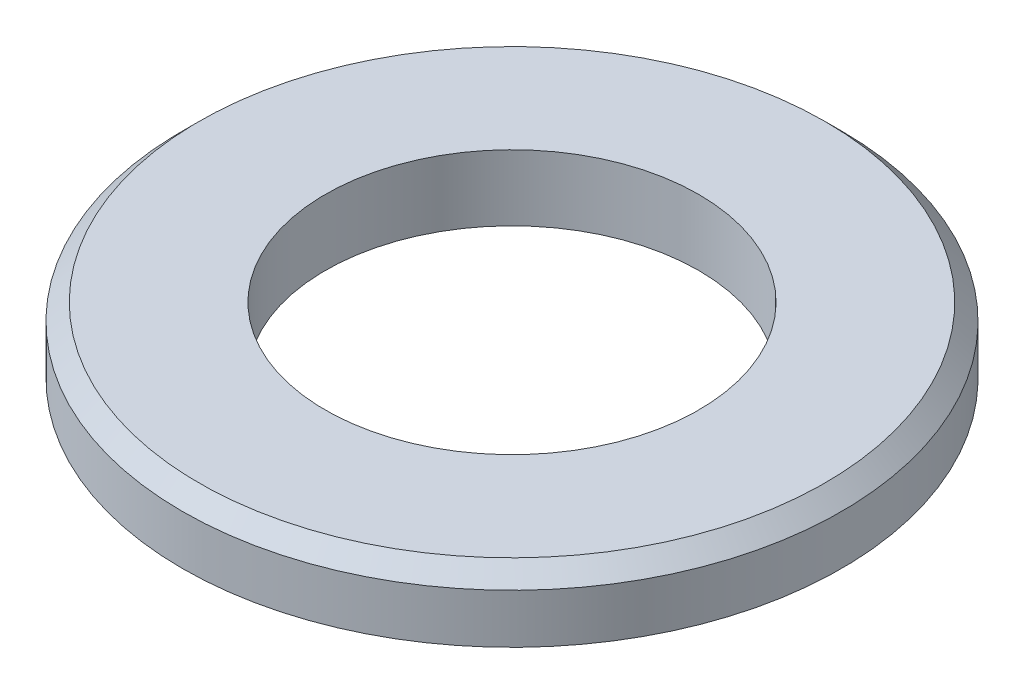
SolidWorks part; units mm, degrees
material "钢"
ref_plane "基准面1" through (0, 0, 0) normal (0, 0, 1) x (1, 0, 0)
ref_plane "基准面2" through (0, 0, 0) normal (0, 1, 0) x (1, 0, 0)
ref_plane "基准面3" through (0, 0, 0) normal (1, 0, 0) x (0, 0, -1)
sketch "尺寸草图" plane through (0, 0, 0) normal (0, 0, 1) x (1, 0, 0)
  line L0 (0, 0) -> (9.1, 0)
  point P3 (3, 0)
  point P4 (30, 0)
  point P5 (17, 0)
  dimension "h" = 3
  dimension "d2" = 30
  dimension "d1" = 17
sketch "草图1" plane through (0, 0, 0) normal (0, 0, 1) x (1, 0, 0)
  line L0 (0, 0) -> (0, 52.7318) construction
  line L1 (-14.25, 11.6445) -> (-15, 10.8945)
  line L2 (-8.5, 8.6445) -> (-15, 8.6445)
  line L3 (-8.5, 8.6445) -> (-8.5, 11.6445)
  line L4 (-8.5, 11.6445) -> (-14.25, 11.6445)
  line L5 (-15, 8.6445) -> (-15, 10.8945)
  point P4 (-15, 11.6445)
  dimension "h" = 3
  dimension "D1" = 8.5
  dimension "D2" = 15
revolve "基体-旋转" add sketch "草图1" angle 360 about L0
equation "\"h@草图1\" = \"h@尺寸草图\""
equation "\"D1@草图1\" = \"d1@尺寸草图\" / 2"
equation "\"D2@草图1\" = \"d2@尺寸草图\" / 2"
equation "\"D5@草图1\" = \"h@草图1\" *0.25"
